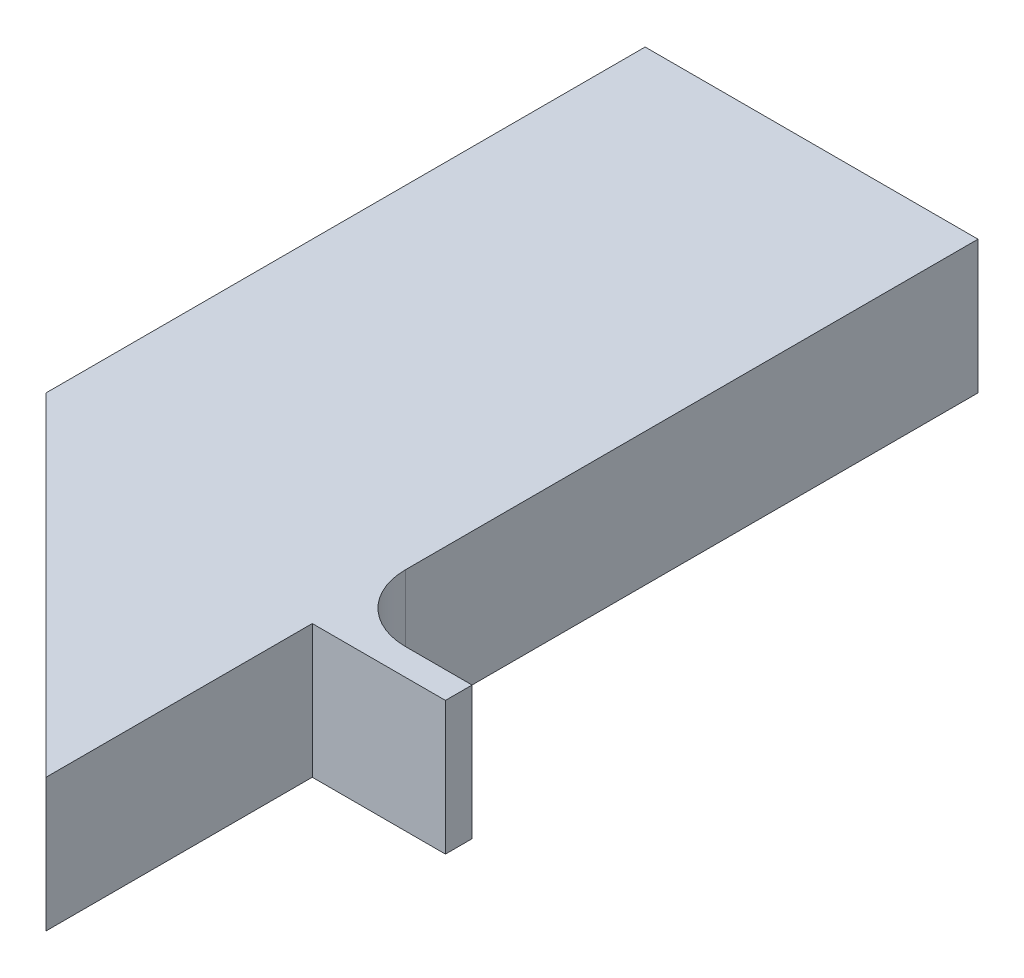
SolidWorks part; units mm, degrees
ref_plane "Front Plane" through (0, 0, 0) normal (0, 0, 1) x (1, 0, 0)
ref_plane "Top Plane" through (0, 0, 0) normal (0, 1, 0) x (1, 0, 0)
ref_plane "Right Plane" through (0, 0, 0) normal (1, 0, 0) x (0, 0, -1)
sketch "Sketch1" plane through (0, 0, 0) normal (0, 1, 0) x (1, 0, 0)
  line L0 (-50, 50) -> (0, 0)
  line L1 (-50, 140) -> (0, 140)
  line L2 (-50, 140) -> (-50, 50)
  line L4 (0, 140) -> (0, 0)
  dimension "D1" = 50
  dimension "D2" = 45
  dimension "D3" = 140
extrude "Boss-Extrude1" add sketch "Sketch1" along normal blind 20
sketch "Sketch2" plane through (0, 0, 0) normal (1, 0, 0) x (0, 0, -1)
  line L0 (0, 20) -> (140, 20) construction
  line L1 (40, 20) -> (44, 20)
  line L2 (40, 20) -> (40, 0)
  line L3 (40, 0) -> (44, 0)
  line L4 (44, 20) -> (44, 0)
  line L5 (0, 0) -> (140, 0) construction
  line L6 (0, 20) -> (0, 0) construction
  dimension "D1" = 40
  dimension "D2" = 4
extrude "Boss-Extrude2" add sketch "Sketch2" along normal blind 20
sketch "Sketch3" plane through (-50, 0, 0) normal (-1, 0, 0) x (0, 0, 1)
  line L0 (0, 20) -> (0, 0) construction
  line L1 (-46, 16) -> (0, 16)
  line L2 (-46, 16) -> (-46, 4)
  line L3 (-46, 4) -> (0, 4)
  line L4 (0, 16) -> (0, 4)
  line L5 (-50, 20) -> (0, 20) construction
  line L6 (-50, 0) -> (0, 0) construction
  line L7 (-50, 20) -> (-50, 0) construction
  dimension "D1" = 4
  dimension "D2" = 4
  dimension "D3" = 4
extrude "Cut-Extrude1" cut sketch "Sketch3" against normal offset from surface (46 mm away) 4 up to face at (0, 10, -20)
sketch "Sketch4" plane through (0, 0, 0) normal (0, -1, 0) x (1, 0, 0)
  line L0 (-25, -140) -> (-25, -25) construction
  line L3 (20, -44) -> (0, -44) construction
  line L4 (0, -140) -> (-50, -140) construction
  line L5 (-50, -50) -> (0, 0) construction
  line L6 (-50, -140) -> (-50, -50) construction
  circle A0 centre (-25, -54) radius 11
  circle A1 centre (-25, -114) radius 11
  dimension "D1" = 22
  dimension "D2" = 22
  dimension "D3" = 10
  dimension "D4" = 60
  dimension "D5" = 25
extrude "Cut-Extrude2" cut sketch "Sketch4" against normal blind 8
fillet "Fillet1" radius 10 1 edges at (0, 10, -44)
